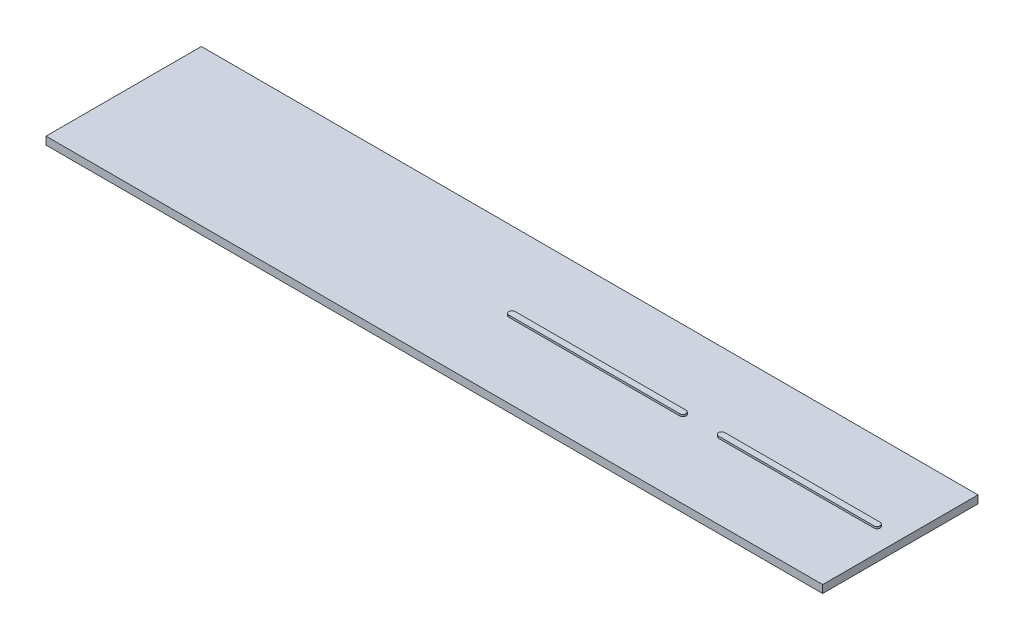
SolidWorks part; units mm, degrees
ref_plane "Front Plane" through (0, 0, 0) normal (0, 0, 1) x (1, 0, 0)
ref_plane "Top Plane" through (0, 0, 0) normal (0, 1, 0) x (1, 0, 0)
ref_plane "Right Plane" through (0, 0, 0) normal (1, 0, 0) x (0, 0, -1)
sketch "Sketch1" plane through (0, 0, 0) normal (0, 1, 0) x (1, 0, 0)
  line L1 (-50000, 10000) -> (50000, 10000)
  line L2 (-50000, 10000) -> (-50000, -10000)
  line L3 (-50000, -10000) -> (50000, -10000)
  line L4 (50000, 10000) -> (50000, -10000)
  point P4 (0, 10000)
  point P7 (-50000, 0)
  dimension "D1" = 100000
  dimension "D2" = 20000
extrude "Boss-Extrude1" add sketch "Sketch1" against normal blind 1000
sketch "Sketch2" plane through (0, 0, 0) normal (0, 1, 0) x (1, 0, 0)
  line L0 (47000, 0) -> (27000, 0) construction
  line L1 (47000, -400) -> (27000, -400)
  line L2 (47000, 400) -> (27000, 400)
  line L3 (0, 0) -> (22000, 0) construction
  line L4 (0, 400) -> (22000, 400)
  line L5 (0, -400) -> (22000, -400)
  arc A0 (47000, -400) -> (47000, 400) centre (47000, 0) ccw
  arc A1 (27000, 400) -> (27000, -400) centre (27000, 0) ccw
  arc A2 (0, 400) -> (0, -400) centre (0, 0) ccw
  arc A3 (22000, -400) -> (22000, 400) centre (22000, 0) ccw
  point P3 (37000, 0)
  point P8 (11000, 0)
  dimension "D3" = 5000
  dimension "D1" = 800
  dimension "D2" = 800
  dimension "D4" = 22000
  dimension "D5" = 20000
extrude "Boss-Extrude2" add sketch "Sketch2" along normal blind 250
